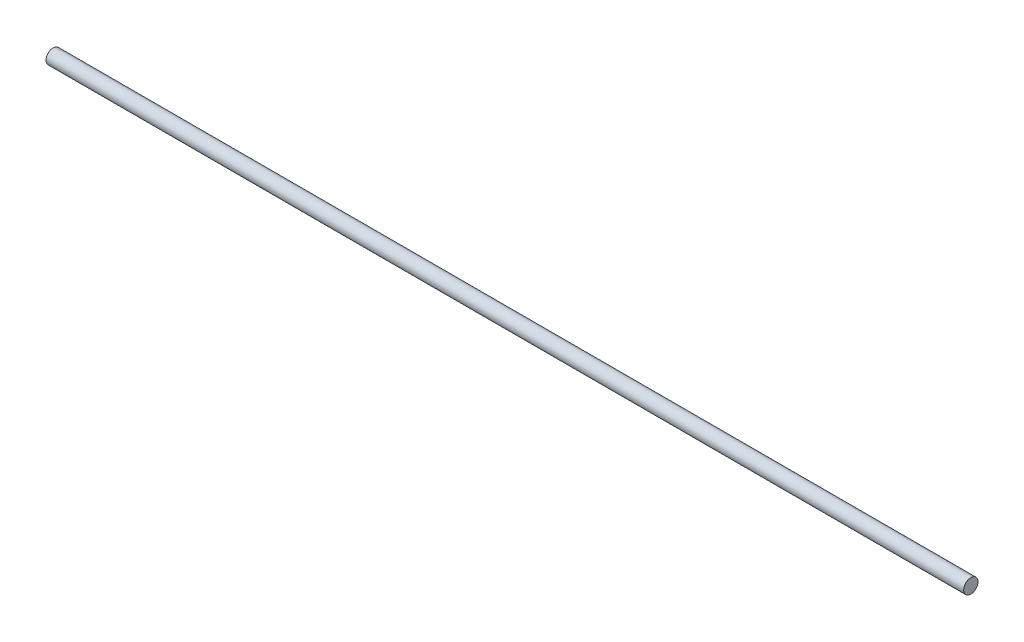
SolidWorks part; units mm, degrees
ref_plane "Front Plane" through (0, 0, 0) normal (0, 0, 1) x (1, 0, 0)
ref_plane "Top Plane" through (0, 0, 0) normal (0, 1, 0) x (1, 0, 0)
ref_plane "Right Plane" through (0, 0, 0) normal (1, 0, 0) x (0, 0, -1)
sketch "Sketch1" plane through (0, 0, 0) normal (0, 1, 0) x (1, 0, 0)
  line L0 (0, 0) -> (-1219.2, 0)
  dimension "D1" = 1219.2
sweep "Sweep1" add path "Sketch1" circular profile diameter 19.05 parameters "D3"=19.05
